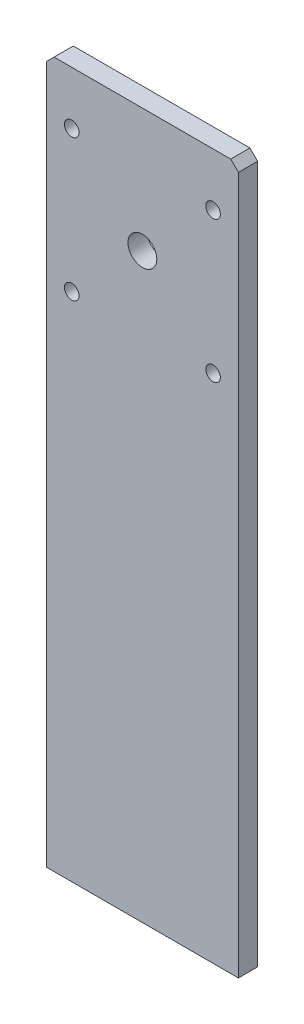
SolidWorks part; units mm, degrees
material "6061 Alloy"
ref_plane "Front Plane" through (0, 0, 0) normal (0, 0, 1) x (1, 0, 0)
ref_plane "Top Plane" through (0, 0, 0) normal (0, 1, 0) x (1, 0, 0)
ref_plane "Right Plane" through (0, 0, 0) normal (1, 0, 0) x (0, 0, -1)
sketch "Sketch1" plane through (0, 0, 0) normal (0, 0, 1) x (1, 0, 0)
  line L0 (31.75, 0) -> (31.75, 192.3796) construction
  line L1 (0, 0) -> (63.5, 0)
  line L2 (0, 0) -> (0, 233.2736)
  line L3 (0, 233.2736) -> (63.5, 233.2736)
  line L4 (63.5, 0) -> (63.5, 233.2736)
  line L5 (8.382, 215.7476) -> (55.118, 215.7476) construction
  line L6 (3.556, 220.5736) -> (59.944, 220.5736) construction
  line L7 (3.556, 220.5736) -> (3.556, 164.1856) construction
  line L8 (3.556, 164.1856) -> (59.944, 164.1856) construction
  line L9 (59.944, 220.5736) -> (59.944, 164.1856) construction
  line L10 (3.556, 220.5736) -> (59.944, 164.1856) construction
  line L11 (3.556, 164.1856) -> (59.944, 220.5736) construction
  line L12 (55.118, 215.7476) -> (55.118, 169.0116) construction
  line L13 (8.382, 169.0116) -> (55.118, 169.0116) construction
  line L14 (8.382, 215.7476) -> (8.382, 169.0116) construction
  line L15 (20.3517, 102.0699) -> (20.3518, 51.3842) construction
  line L16 (43.1482, 108.5723) -> (43.1483, 59.5249) construction
  line L17 (43.1483, 59.5249) -> (63.5, 59.5249) construction
  line L18 (12.5285, 0) -> (12.5285, 18.0677) construction
  line L19 (50.9715, 0) -> (50.9715, 26.3499) construction
  circle A0 centre (8.382, 215.7476) radius 2.413
  circle A1 centre (55.118, 215.7476) radius 2.413
  circle A2 centre (8.382, 169.0116) radius 2.413
  circle A3 centre (55.118, 169.0116) radius 2.413
  circle A4 centre (20.3517, 102.0699) radius 1.9177 construction
  circle A5 centre (43.1482, 108.5723) radius 1.9177 construction
  circle A6 centre (31.75, 192.3796) radius 4.7625
  circle A7 centre (20.3518, 51.3842) radius 1.9177 construction
  circle A8 centre (43.1483, 59.5249) radius 1.9177 construction
  dimension "D4" = 4.826
  dimension "D7" = 3.8354
  dimension "D10" = 9.525
  dimension "D12" = 51.3842
  dimension "D1" = 63.5
  dimension "D2" = 56.388
  dimension "D3" = 4.826
  dimension "D5" = 12.7
  dimension "D6" = 192.3796
  dimension "D8" = 102.0699
  dimension "D9" = 7.8232
  dimension "D11" = 19.2215
  dimension "D13" = 59.5249
  dimension "D14" = 108.5723
  dimension "D15" = 19.2215
  dimension "D16" = 7.8232
extrude "Boss-Extrude1" add sketch "Sketch1" along normal blind 6.35
fillet "Fillet1" [suppressed] radius 19.05
ref_plane "Center plane" through (31.75, 0, 0) normal (1, 0, 0) x (0, 0, -1)
chamfer "Chamfer1" distance 2.54 angle 45 2 edges at (0, 233.2736, 3.175) (63.5, 233.2736, 3.175)
equation "\"bolt diameter\"= 0.2"
equation "\"stepper body width\"= 2.22"
equation "\"stepper mount offset\"= 0.19"
equation "\"stepper mount diameter\"= 0.19"
equation "\"D2@Sketch1\"=\"stepper body width\""
equation "\"D3@Sketch1\"=\"stepper mount offset\""
equation "\"D4@Sketch1\"=\"stepper mount diameter\""
equation "\"thin metal\"= 0.12"
equation "\"thick metal\"= 0.25"
equation "\"y axis stepper wall bracket thickness\"= 1"
equation "\"y axis stepper wall mount side offset\"= 1/2"
equation "\"y axis stepper wall mount top offset\"= 1/2"
equation "\"y axis stepper wall width\"= \"stepper body width\" + 1                  "
equation "\"y axis stepper wall height off base\"= 8"
equation "\"D6@Sketch1\"=0.454 + 2 * \"thin metal\" + \"recognizer arm height to hole\" + 2 + \"recognizer nut plate height\" / 2"
equation "\"base length\"= 21"
equation "\"stepper shaft offset from body\"= 0.79"
equation "\"recognizer width\"= 2.5"
equation "\"recognizer nut plate height\"= 1.25"
equation "\"base width\"= 16.5"
equation "\"glass pane length\"= 14.125"
equation "\"glass pane width\"= 10.1875"
equation "\"glass pane wall width\"= 3/4"
equation "\"glass lip\"= 1/4"
equation "\"stepper spacer thickness\"= 0.2"
equation "\"recognizer nut plate offset\"= 1.5"
equation "\"recognizer bracket length\"= 4"
equation "\"recognizer arm height to hole\"= 4.255"
equation "\"x axis threaded rod length\"= 3"
